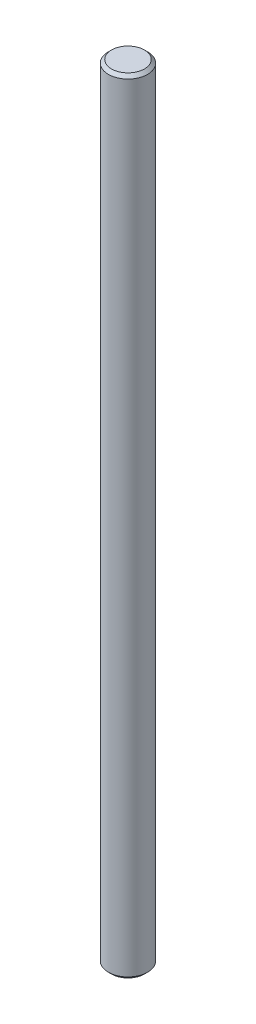
SolidWorks part; units mm, degrees
ref_plane "Front" through (0, 0, 0) normal (0, 0, 1) x (1, 0, 0)
ref_plane "Top" through (0, 0, 0) normal (0, 1, 0) x (1, 0, 0)
ref_plane "Right" through (0, 0, 0) normal (1, 0, 0) x (0, 0, -1)
sketch "Sketch1" plane through (0, 0, 0) normal (0, 1, 0) x (1, 0, 0)
  circle A0 centre (0, 0) radius 2.5
extrude "Extrude1" add sketch "Sketch1" along normal blind 100
chamfer "Chamfer1" distance 0.4 angle 45 2 edges at (0, 0, 2.5) (0, 100, 2.5)
